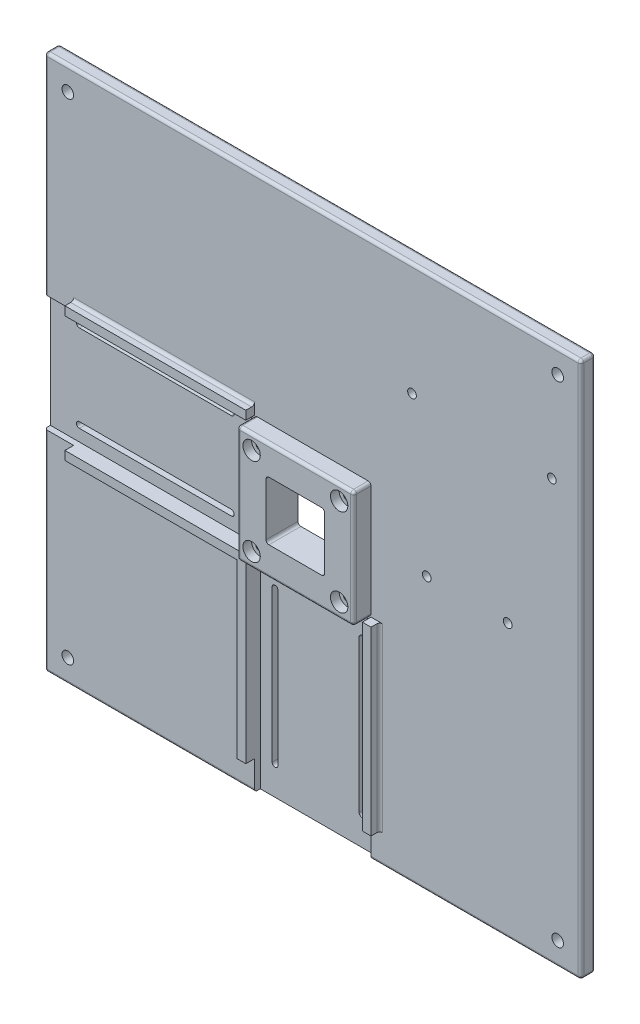
SolidWorks part; units mm, degrees
ref_plane "Plan de face" through (0, 0, 0) normal (0, 0, 1) x (1, 0, 0)
ref_plane "Plan de dessus" through (0, 0, 0) normal (0, 1, 0) x (1, 0, 0)
ref_plane "Plan de droite" through (0, 0, 0) normal (1, 0, 0) x (0, 0, -1)
sketch "Esquisse1" plane through (0, 0, 0) normal (0, 0, 1) x (1, 0, 0)
  line L1 (-92.5, 92.5) -> (92.5, 92.5)
  line L2 (-92.5, 92.5) -> (-92.5, -92.5)
  line L3 (-92.5, -92.5) -> (92.5, -92.5)
  line L4 (92.5, 92.5) -> (92.5, -92.5)
  dimension "D1" = 92.5
  dimension "D2" = 185
  dimension "D3" = 92.5
  dimension "D4" = 185
extrude "Boss.-Extru.1" add sketch "Esquisse1" along normal blind 5
fillet "Congé1" radius 1 12 edges at (0, -92.5, 5) (-92.5, 0, 5) (0, 92.5, 5) (92.5, 0, 5) (-92.5, -92.5, 2.5) (92.5, -92.5, 2.5) (-92.5, 92.5, 2.5) (92.5, 92.5, 2.5) (0, -92.5, 0) (-92.5, 0, 0) (0, 92.5, 0) (92.5, 0, 0)
sketch "Esquisse4" plane through (0, 0, 5) normal (0, 0, 1) x (1, 0, 0)
  line L1 (-10.1, 10.1) -> (10.1, 10.1)
  line L2 (-10.1, 10.1) -> (-10.1, -10.1)
  line L3 (-10.1, -10.1) -> (10.1, -10.1)
  line L4 (10.1, 10.1) -> (10.1, -10.1)
  circle A0 centre (-15.1, 15.1) radius 1.6
  circle A1 centre (15.1, 15.1) radius 1.6
  circle A2 centre (15.1, -15.1) radius 1.6
  circle A3 centre (-15.1, -15.1) radius 1.6
  point P4 (0, 0)
  dimension "D5" = 3.2
  dimension "D1" = 10.1
  dimension "D2" = 20.2
  dimension "D3" = 10.1
  dimension "D4" = 20.2
  dimension "D6" = 5
  dimension "D7" = 5
  dimension "D8" = 5
  dimension "D9" = 5
sketch "Esquisse9" plane through (0, 0, 0) normal (0, 0, -1) x (-1, 0, 0)
  line L0 (-92.5, -92.5) -> (-92.5, 92.5) construction
  line L1 (92.5, -92.5) -> (-92.5, -92.5) construction
  line L2 (-92.5, 92.5) -> (92.5, 92.5) construction
  line L3 (92.5, 92.5) -> (92.5, -92.5) construction
  circle A0 centre (-84.5, 84.5) radius 2
  circle A1 centre (84.5, 84.5) radius 2
  circle A2 centre (84.5, -84.5) radius 2
  circle A3 centre (-84.5, -84.5) radius 2
  dimension "D2" = 4
  dimension "D5" = 8
  dimension "D6" = 8
  dimension "D7" = 8
  dimension "D8" = 8
extrude "Enlèv. mat.-Extru.4" cut sketch "Esquisse9" against normal up to next
extrude "Enlèv. mat.-Extru.5" cut sketch "Esquisse4" against normal through all and the other way through all
sketch "Esquisse11" plane through (0, 0, 5) normal (0, 0, 1) x (1, 0, 0)
  line L0 (-10.1, -10.1) -> (10.1, -10.1) construction
  line L1 (-20.1, -20.1) -> (20.1, -20.1)
  line L2 (-20.1, -20.1) -> (-20.1, 20.1)
  line L3 (-20.1, 20.1) -> (20.1, 20.1)
  line L4 (20.1, -20.1) -> (20.1, 20.1)
  line L5 (-10.1, 10.1) -> (-10.1, -10.1) construction
  line L6 (10.1, 10.1) -> (-10.1, 10.1) construction
  line L7 (10.1, -10.1) -> (10.1, 10.1) construction
  dimension "D1" = 10
  dimension "D2" = 10
  dimension "D3" = 10
  dimension "D4" = 10
extrude "Boss.-Extru.3" add sketch "Esquisse11" along normal blind 6 contours L2 L3 L4 L1
fillet "Congé2" radius 1 12 edges at (10.1, -10.1, 2.5) (-10.1, -10.1, 2.5) (10.1, 10.1, 2.5) (-10.1, 10.1, 2.5) (-20.1, 0, 11) (0, 20.1, 11) (20.1, 0, 11) (0, -20.1, 11) (20.1, 20.1, 8) (20.1, -20.1, 8) (-20.1, -20.1, 8) (-20.1, 20.1, 8)
sketch "Esquisse12" plane through (0, 0, 11) normal (0, 0, 1) x (1, 0, 0)
  line L0 (-9.1, -10.1) -> (9.1, -10.1) construction
  line L1 (-9.1, -10.1) -> (9.1, -10.1)
  line L4 (19.1, 19.1) -> (-19.1, 19.1)
  line L5 (19.1, 19.1) -> (-19.1, 19.1)
  line L6 (-19.1, 19.1) -> (-19.1, -19.1)
  line L7 (-19.1, 19.1) -> (-19.1, -19.1)
  line L12 (10.1, -9.1) -> (10.1, 9.1)
  line L13 (-9.1, -10.1) -> (9.1, -10.1)
  line L14 (-10.1, 9.1) -> (-10.1, -9.1)
  line L15 (9.1, 10.1) -> (-9.1, 10.1)
  line L16 (10.1, -9.1) -> (10.1, 9.1)
  line L17 (-9.1, -10.1) -> (9.1, -10.1)
  line L18 (-10.1, 9.1) -> (-10.1, -9.1)
  line L19 (9.1, 10.1) -> (-9.1, 10.1)
  line L22 (-19.1, -19.1) -> (19.1, -19.1)
  line L23 (-19.1, -19.1) -> (19.1, -19.1)
  line L24 (19.1, -19.1) -> (19.1, 19.1)
  line L25 (19.1, -19.1) -> (19.1, 19.1)
  circle A0 centre (-15.1, -15.1) radius 1.6 construction
  circle A1 centre (15.1, -15.1) radius 1.6 construction
  circle A2 centre (15.1, 15.1) radius 1.6 construction
  circle A3 centre (-15.1, 15.1) radius 1.6 construction
  circle A4 centre (-15.1, -15.1) radius 1.6
  circle A5 centre (15.1, -15.1) radius 1.6
  circle A6 centre (15.1, 15.1) radius 1.6
  circle A7 centre (-15.1, 15.1) radius 1.6
  arc A12 (9.1, -10.1) -> (10.1, -9.1) centre (9.1, -9.1) ccw
  arc A13 (-10.1, -9.1) -> (-9.1, -10.1) centre (-9.1, -9.1) ccw
  arc A14 (-9.1, 10.1) -> (-10.1, 9.1) centre (-9.1, 9.1) ccw
  arc A15 (10.1, 9.1) -> (9.1, 10.1) centre (9.1, 9.1) ccw
  arc A16 (9.1, -10.1) -> (10.1, -9.1) centre (9.1, -9.1) ccw
  arc A17 (-10.1, -9.1) -> (-9.1, -10.1) centre (-9.1, -9.1) ccw
  arc A18 (-9.1, 10.1) -> (-10.1, 9.1) centre (-9.1, 9.1) ccw
  arc A19 (10.1, 9.1) -> (9.1, 10.1) centre (9.1, 9.1) ccw
  dimension "D1" = 0
  dimension "D2" = 0
extrude "Enlèv. mat.-Extru.6" cut sketch "Esquisse12" against normal through all contours L16 A19 L19 A18 L18 A17 L1 A16 | A6 | A7 | A5 | A4
sketch "Esquisse13" plane through (0, 0, 11) normal (0, 0, 1) x (1, 0, 0)
  circle A0 centre (-15.1, 15.1) radius 3
  circle A1 centre (15.1, 15.1) radius 3
  circle A2 centre (15.1, -15.1) radius 3
  circle A3 centre (-15.1, -15.1) radius 3
  dimension "D1" = 6
extrude "Enlèv. mat.-Extru.7" cut sketch "Esquisse13" against normal blind 3
sketch "Esquisse14" plane through (0, 0, 5) normal (0, 0, 1) x (1, 0, 0)
  line L0 (-82.5, 15) -> (-30.1, 15) construction
  line L1 (-82.5, 16) -> (-30.1, 16)
  line L2 (-82.5, 14) -> (-30.1, 14)
  line L3 (-92.5, -91.5) -> (-92.5, 91.5) construction
  line L4 (-20.1, -19.1) -> (-20.1, 19.1) construction
  line L5 (-30.1, -15) -> (-82.5, -15) construction
  line L6 (-30.1, -16) -> (-82.5, -16)
  line L7 (-30.1, -14) -> (-82.5, -14)
  line L8 (15, -30.1) -> (15, -82.5) construction
  line L9 (16, -30.1) -> (16, -82.5)
  line L10 (14, -30.1) -> (14, -82.5)
  line L11 (-15, -82.5) -> (-15, -30.1) construction
  line L12 (-16, -82.5) -> (-16, -30.1)
  line L13 (-14, -82.5) -> (-14, -30.1)
  line L14 (-19.1, -20.1) -> (19.1, -20.1) construction
  line L15 (91.5, -92.5) -> (-91.5, -92.5) construction
  arc A0 (-82.5, 16) -> (-82.5, 14) centre (-82.5, 15) ccw
  arc A1 (-30.1, 14) -> (-30.1, 16) centre (-30.1, 15) ccw
  arc A2 (-30.1, -16) -> (-30.1, -14) centre (-30.1, -15) ccw
  arc A3 (-82.5, -14) -> (-82.5, -16) centre (-82.5, -15) ccw
  arc A4 (16, -30.1) -> (14, -30.1) centre (15, -30.1) ccw
  arc A5 (14, -82.5) -> (16, -82.5) centre (15, -82.5) ccw
  arc A6 (-16, -82.5) -> (-14, -82.5) centre (-15, -82.5) ccw
  arc A7 (-14, -30.1) -> (-16, -30.1) centre (-15, -30.1) ccw
  point P2 (-56.3, 15)
  point P11 (-20.1, 0)
  point P14 (-56.3, -15)
  point P21 (15, -56.3)
  point P26 (-15, -56.3)
  point P33 (0, -20.1)
  dimension "D1" = 2
  dimension "D2" = 10
  dimension "D3" = 10
  dimension "D4" = 15
  dimension "D5" = 2
  dimension "D6" = 10
  dimension "D7" = 10
  dimension "D8" = 30
  dimension "D9" = 2
  dimension "D10" = 2
  dimension "D11" = 15
  dimension "D12" = 30
  dimension "D13" = 10
  dimension "D14" = 10
  dimension "D15" = 10
  dimension "D16" = 10
extrude "Enlèv. mat.-Extru.8" cut sketch "Esquisse14" against normal through all
sketch "Esquisse15" plane through (0, 0, 5) normal (0, 0, 1) x (1, 0, 0)
  line L0 (-20.1, -20.1) -> (-20.1, -82.5)
  line L1 (-20.1, 20.1) -> (-82.5, 20.1)
  line L2 (-20.1, 20.1) -> (-20.1, 23.1)
  line L3 (-20.1, 23.1) -> (-82.5, 23.1)
  line L4 (-82.5, 20.1) -> (-82.5, 23.1)
  line L5 (-20.1, -20.1) -> (-82.5, -20.1)
  line L7 (-23.1, -23.1) -> (-82.5, -23.1)
  line L8 (-82.5, -20.1) -> (-82.5, -23.1)
  line L9 (-20.1, -82.5) -> (-23.1, -82.5)
  line L10 (-23.1, -82.5) -> (-23.1, -23.1)
  line L12 (23.1, -20.1) -> (20.1, -20.1)
  line L13 (23.1, -20.1) -> (23.1, -82.5)
  line L14 (23.1, -82.5) -> (20.1, -82.5)
  line L15 (20.1, -20.1) -> (20.1, -82.5)
  dimension "D1" = 3
  dimension "D2" = 3
  dimension "D3" = 3
  dimension "D4" = 3
  dimension "D5" = 20.1
  dimension "D6" = 40.2
  dimension "D7" = 20.1
  dimension "D8" = 40.2
extrude "Boss.-Extru.4" add sketch "Esquisse15" along normal blind 3
fillet "Congé3" radius 1 4 edges at (-51.3, 23.1, 5) (-52.8, -23.1, 5) (-23.1, -52.8, 5) (23.1, -51.3, 5)
sketch "Esquisse20" plane through (0, 0, 5) normal (0, 0, 1) x (1, 0, 0)
  line L0 (-91.5, 92.5) -> (91.5, 92.5) construction
  line L1 (92.5, 91.5) -> (92.5, -91.5) construction
  circle A1 centre (39.32, 1.7) radius 1.5
  circle A5 centre (34.24, 53.77) radius 1.5
  circle A6 centre (82.5, 52.5) radius 1.5
  circle A7 centre (67.26, 1.7) radius 1.5
  dimension "D1" = 3
  dimension "D2" = 3
  dimension "D3" = 3
  dimension "D4" = 3
  dimension "D6" = 48.26
  dimension "D8" = 15.24
  dimension "D9" = 1.27
  dimension "D10" = 40
  dimension "D11" = 10
  dimension "D5" = 27.94
  dimension "D7" = 50.8
extrude "Enlèv. mat.-Extru.12" cut sketch "Esquisse20" against normal blind 10
sketch "Esquisse21" plane through (0, 0, 5) normal (0, 0, 1) x (1, 0, 0)
  line L1 (-95.7156, 20.1) -> (-21.1, 20.1)
  line L2 (-95.7156, 20.1) -> (-95.7156, -20.1)
  line L3 (-95.7156, -20.1) -> (-21.1, -20.1)
  line L9 (-82.5, 20.1) -> (-20.1, 20.1) construction
  line L10 (-20.1, -20.1) -> (-82.5, -20.1) construction
  line L11 (-21.1, 20.1) -> (-21.1, -20.1)
  line L12 (-20.1, -19.1) -> (-20.1, 19.1) construction
  dimension "D1" = 1
extrude "Enlèv. mat.-Extru.13" cut sketch "Esquisse21" against normal blind 2
sketch "Esquisse22" plane through (0, 0, 5) normal (0, 0, 1) x (1, 0, 0)
  line L5 (-20.1, -82.5) -> (-20.1, -20.1) construction
  line L7 (20.1, -21.1) -> (20.1, -100.2038)
  line L8 (20.1, -100.2038) -> (-20.1, -100.2038)
  line L9 (-20.1, -21.1) -> (-20.1, -100.2038)
  line L10 (20.1, -20.1) -> (20.1, -82.5) construction
  line L11 (-20.1, -21.1) -> (20.1, -21.1)
  dimension "D1" = 1
extrude "Enlèv. mat.-Extru.20" cut sketch "Esquisse22" against normal blind 2
